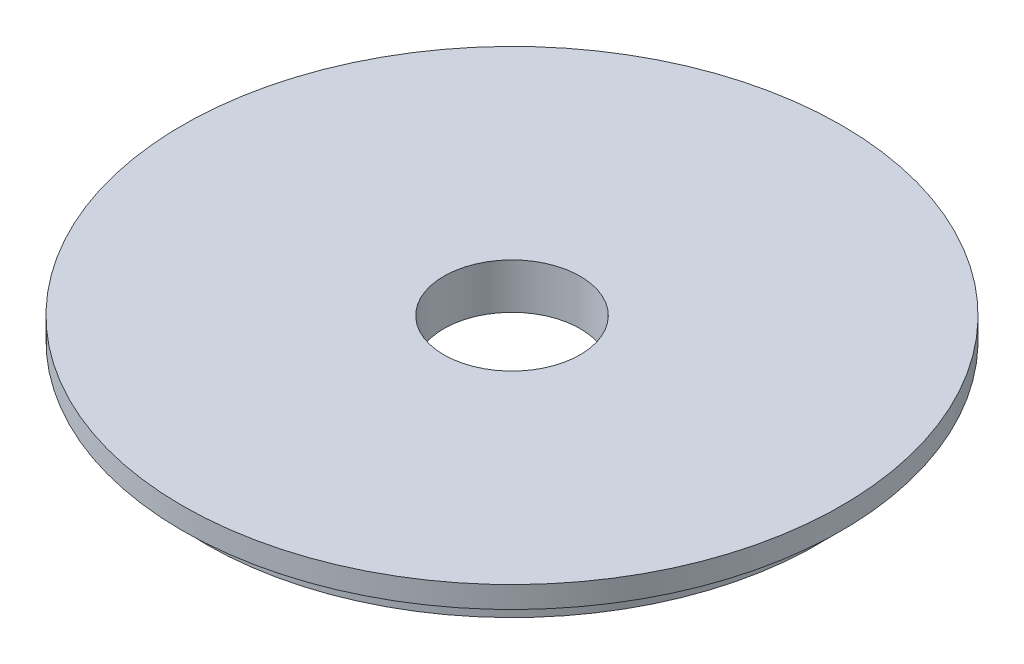
SolidWorks part; units mm, degrees
material "Phenolic Fiber Filled"
ref_plane "Front Plane" through (0, 0, 0) normal (0, 0, 1) x (1, 0, 0)
ref_plane "Top Plane" through (0, 0, 0) normal (0, 1, 0) x (1, 0, 0)
ref_plane "Right Plane" through (0, 0, 0) normal (1, 0, 0) x (0, 0, -1)
sketch "Sketch1" plane through (0, 0, 0) normal (0, 0, 1) x (1, 0, 0)
  line L0 (0, 0) -> (-9.525, 0) construction
  line L1 (-9.525, 0) -> (-46.0756, 0)
  line L2 (-46.0756, 0) -> (-46.0756, -3.0226)
  line L3 (-46.0756, -3.0226) -> (-42.7482, -3.0226)
  line L4 (-42.7482, -3.0226) -> (-42.7482, -6.35)
  line L5 (-42.7482, -6.35) -> (-9.525, -6.35)
  line L6 (-9.525, -6.35) -> (-9.525, 0)
  line L7 (0, 0) -> (0, -5.0066) construction
  dimension "D1" = 9.525
  dimension "D2" = 46.0756
  dimension "D3" = 42.7482
  dimension "D4" = 6.35
  dimension "D5" = 3.0226
revolve "Revolve1" add sketch "Sketch1" angle 360 about L7
